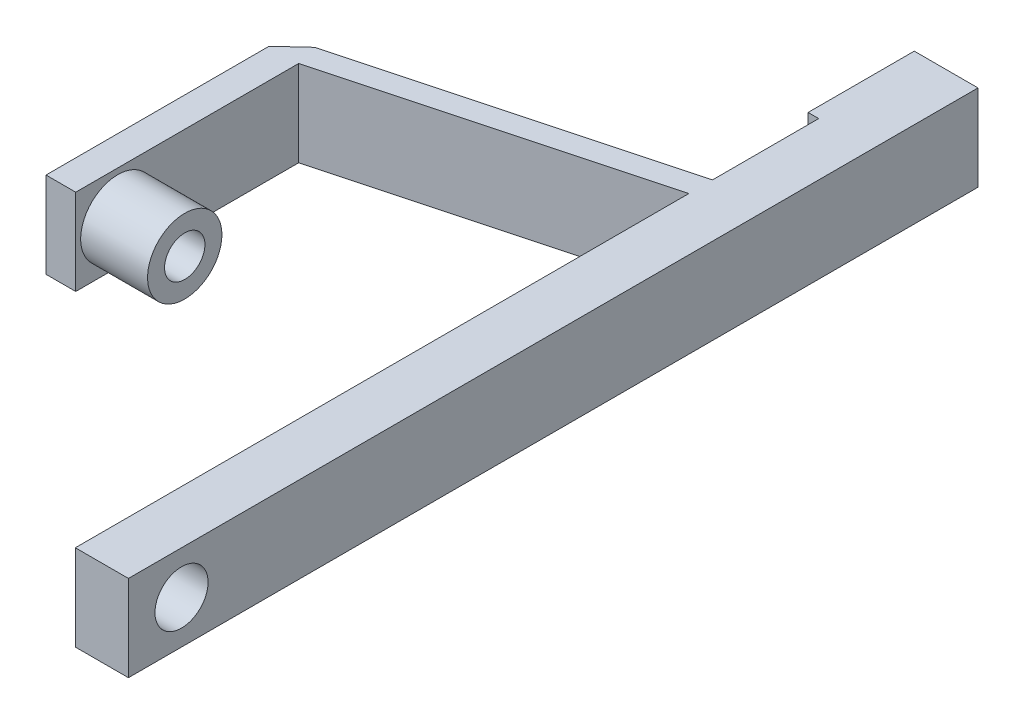
SolidWorks part; units mm, degrees
ref_plane "Front Plane" through (0, 0, 0) normal (0, 0, 1) x (1, 0, 0)
ref_plane "Top Plane" through (0, 0, 0) normal (0, 1, 0) x (1, 0, 0)
ref_plane "Right Plane" through (0, 0, 0) normal (1, 0, 0) x (0, 0, -1)
ref_plane "Plane1"
sketch "Sketch1" plane through (0, 0, 0) normal (0, 1, 0) x (-1, 0, 0)
  line L0 (0, 0) -> (12.7, 0)
  line L1 (12.7, 0) -> (12.7, -177.8)
  line L2 (12.7, -177.8) -> (0, -177.8)
  line L3 (0, -177.8) -> (0, 0)
  dimension "D1" = 12.7
  dimension "D2" = 177.8
extrude "Extrusion1" add sketch "Sketch1" along normal blind 20.574
sketch "Sketch2" plane through (-12.7, 0, 0) normal (-1, 0, 0) x (0, 0, 1)
  line L0 (-121.3597, 12.319) -> (-121.3597, 8.255)
  line L1 (-121.3597, 8.255) -> (-107.4405, 8.255)
  line L2 (-107.4405, 8.255) -> (-107.4405, 12.319)
  line L3 (-107.4405, 12.319) -> (-121.3597, 12.319)
  line L4 (-107.4405, 8.255) -> (-107.4405, 0)
  line L5 (-107.4405, 0) -> (-103.3765, 0)
  line L6 (-103.3765, 0) -> (-103.3765, 20.574)
  line L7 (-103.3765, 20.574) -> (-107.4405, 20.574)
  line L8 (-107.4405, 20.574) -> (-107.4405, 12.319)
  line L9 (-107.4405, 12.319) -> (-107.4405, 8.255)
  dimension "D1" = 121.6401
  dimension "D2" = 4.064
  dimension "D3" = 13.9192
  dimension "D4" = 4.064
sketch "Sketch3" plane through (0, 0, 0) normal (0, -1, 0) x (1, 0, 0)
  line L0 (-12.7, -146.7612) -> (-86.3035, -127.0392)
  line L1 (-86.3035, -127.0392) -> (-86.3035, -73.6992)
  line L2 (-86.3035, -73.6992) -> (-93.4155, -73.6992)
  line L3 (-93.4155, -73.6992) -> (-93.4155, -127.0392)
  line L4 (-93.4155, -127.0392) -> (-87.7132, -132.3003)
  line L5 (-87.7132, -132.3003) -> (-12.7, -152.4)
  line L6 (-12.7, -152.4) -> (-12.7, -177.8)
  line L7 (-12.7, -177.8) -> (0, -177.8)
  line L8 (0, -177.8) -> (0, -146.7612)
  line L9 (0, -146.7612) -> (-12.7, -146.7612)
  line L10 (-12.7, -177.8) -> (0, -177.8)
  line L11 (0, -177.8) -> (0, -146.7612)
  line L12 (0, -146.7612) -> (-12.7, -146.7612)
  line L13 (-12.7, -146.7612) -> (-12.7, -177.8)
  line M3 (-12.7, 0) -> (-12.7, -177.8)
  dimension "D1" = 12.7
  dimension "D2" = 31.0388
  dimension "D3" = 76.2
  dimension "D4" = 53.34
  dimension "D5" = 7.112
  dimension "D6" = 152.9283
  dimension "D7" = 177.8
extrude "Extrusion3" add sketch "Sketch3" against normal blind 20.32 contours L4 L5 L0 L1 L2 L3 M3
sketch "Sketch4" plane through (-12.7, 0, 0) normal (-1, 0, 0) x (0, 0, 1)
  line L0 (0, 20.574) -> (0, 0) construction
  circle A0 centre (-12.7, 10.287) radius 6.35
  dimension "D1" = 12.7
extrude "Extrusion4" cut sketch "Sketch4" against normal blind 20.32
ref_plane "Plane2"
sketch "Sketch5" plane through (0, 20.32, 0) normal (0, 1, 0) x (1, 0, 0)
  line L0 (-86.3035, 73.6992) -> (-86.3035, 127.0392)
  line L1 (-86.3035, 127.0392) -> (-12.7, 146.7612)
  line L2 (-12.7, 146.7612) -> (-12.7, 152.4)
  line L3 (-12.7, 152.4) -> (-87.7132, 132.3003)
  line L4 (-87.7132, 132.3003) -> (-93.4155, 127.0392)
  line L5 (-93.4155, 127.0392) -> (-93.4155, 73.6992)
  line L6 (-93.4155, 73.6992) -> (-86.3035, 73.6992)
  dimension "D1" = 76.2
  dimension "D2" = 5.6388
extrude "Extrusion5" add sketch "Sketch5" along normal blind 0.254
sketch "Sketch6" plane through (-93.4155, 0, 0) normal (-1, 0, 0) x (0, 0, 1)
  line L0 (-73.6992, 0) -> (-73.6992, 20.574)
  line L1 (-73.6992, 20.574) -> (-80.3031, 20.574)
  line L2 (-80.3032, 20.5739) -> (-80.3032, 0.0001)
  line L3 (-80.3031, 0) -> (-73.6992, 0)
  line L4 (-80.3032, 20.574) -> (-80.3032, 0)
  arc A0 (-80.3032, 0) -> (-80.3032, 20.574) centre (-85.0132, 10.287) ccw
  arc A1 (-80.3032, 0.0001) -> (-80.3031, 0) centre (-80.3031, 0.0001) ccw
  arc A2 (-80.3031, 20.574) -> (-80.3032, 20.5739) centre (-80.3031, 20.5739) ccw
  dimension "D2" = 0.0001
  dimension "D3" = 0.0001
  dimension "D1" = 6.604
sketch "Sketch7" plane through (-93.4155, 0, 0) normal (-1, 0, 0) x (0, 0, 1)
  circle A0 centre (-83.7703, 10.287) radius 6.0071
extrude "Extrusion7" cut sketch "Sketch7" against normal blind 0.508
sketch "Sketch8" plane through (-92.9075, 0, 0) normal (-1, 0, 0) x (0, 0, 1)
  circle A0 centre (-83.7703, 10.287) radius 4.826
  dimension "D1" = 9.652
extrude "Extrusion8" cut sketch "Sketch8" against normal blind 22.86
sketch "Sketch9" plane through (-86.3035, 0, 0) normal (1, 0, 0) x (0, 0, -1)
  circle A0 centre (83.7703, 10.287) radius 8.89
  circle A1 centre (83.7703, 10.287) radius 6.0071
  dimension "D1" = 17.78
extrude "Extrusion9" add sketch "Sketch9" along normal blind 16.002
ref_plane "Plane3"
sketch "Sketch10" plane through (-86.3035, 10.287, -83.7703) normal (1, 0, 0) x (0, 0, -1)
  circle A0 centre (0, 0) radius 6.0071
  circle A1 centre (0, 0) radius 4.826
extrude "Extrusion10" add sketch "Sketch10" along normal blind 16.002 contours A0 A1
sketch "Sketch11" plane through (0, 0, -177.8) normal (0, 0, -1) x (-1, 0, 0)
  line L0 (0, 0) -> (12.7, 0)
  line L1 (12.7, 0) -> (12.7, 20.574)
  line L2 (12.7, 20.574) -> (0, 20.574)
  line L3 (0, 20.574) -> (0, 0)
extrude "Extrusion14" add sketch "Sketch11" along normal blind 25.4
sketch "Sketch12" plane through (-12.7, 0, 0) normal (-1, 0, 0) x (0, 0, 1)
  line L0 (-203.2, 0) -> (-177.8, 0)
  line L1 (-177.8, 0) -> (-177.8, 20.574)
  line L2 (-177.8, 20.574) -> (-203.2, 20.574)
  line L3 (-203.2, 20.574) -> (-203.2, 0)
extrude "Extrusion15" add sketch "Sketch12" along normal blind 2.54
